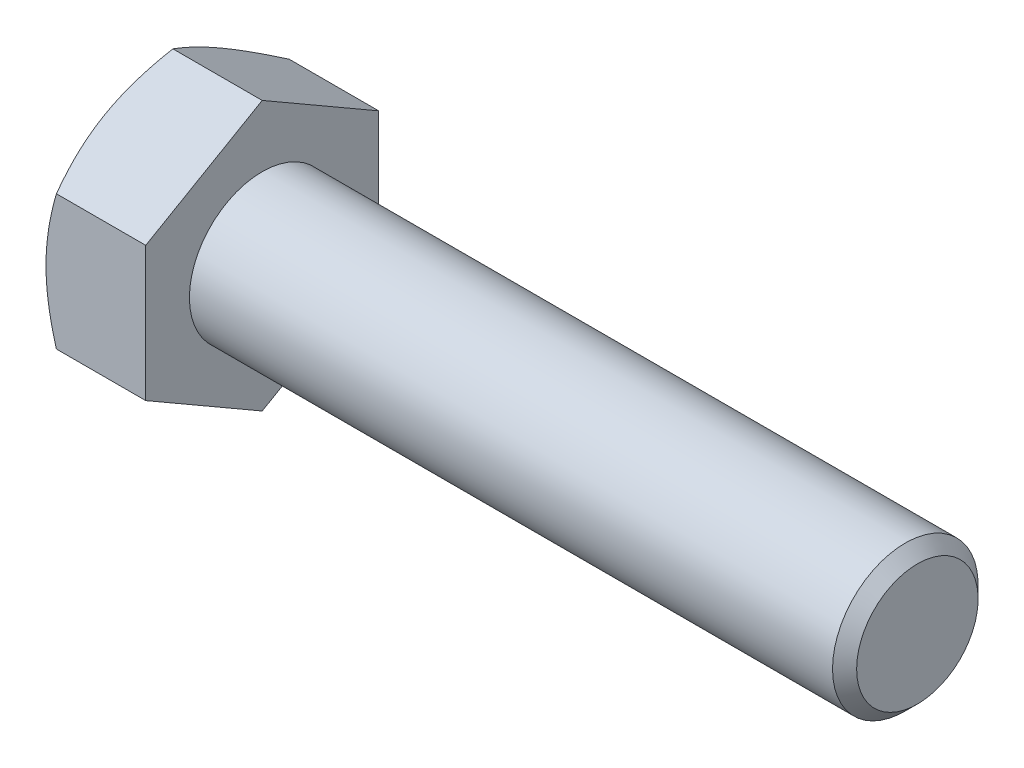
SolidWorks part; units mm, degrees
extrude "BaseHead" add sketch "Sketch1" along normal blind 6.85
sketch "Sketch1" plane through (0, 0, 0) normal (1, 0, 0) x (0, 0, -1)
  line L0 (8, 4.6188) -> (8, -4.6188)
  line L1 (-8, 4.6188) -> (-8, -4.6188)
  line L2 (8, -4.6188) -> (0, -9.2376)
  line L3 (0, -9.2376) -> (-8, -4.6188)
  line L4 (8, 4.6188) -> (0, 9.2376)
  line L5 (0, 9.2376) -> (-8, 4.6188)
  dimension "Width_flats" = 16
  dimension "D2" = 120
  dimension "D3" = 8
  dimension "D4" = 8
  dimension "D5" = 8
ref_plane "Plane1" through (0, 0, 0) normal (0, 0, 1) x (1, 0, 0)
ref_plane "Plane2" through (0, 0, 0) normal (0, 1, 0) x (1, 0, 0)
ref_plane "Plane3" through (0, 0, 0) normal (1, 0, 0) x (0, 0, -1)
sketch "BodySke" plane through (0, 0, 0) normal (0, 0, 1) x (1, 0, 0)
  line L0 (0, 4.6188) -> (0, -4.6188) construction
  line L1 (0, 0) -> (51.85, 0)
  line L2 (0, 0) -> (0, 5)
  line L3 (0, 5) -> (51.022, 5)
  line L4 (51.85, 0) -> (51.85, 4.172)
  line L5 (6.85, 9.2376) -> (6.85, 4.6188) construction
  line L6 (51.85, 4.172) -> (51.022, 5)
  line L7 (0, 0) -> (96.52, 0) construction
  line L8 (51.85, -4.172) -> (51.022, -5) construction
  line L9 (0, -5) -> (51.022, -5) construction
  line L10 (8.35, 15.24) -> (8.35, -1.27) construction
  line L11 (25.85, 15.24) -> (25.85, -1.27) construction
  line L12 (6.85, 4.6188) -> (6.85, -4.6188) construction
  dimension "Diameter" = 10
revolve "BaseBody" add sketch "BodySke"
cosmetic thread "ThreadCosmetic" [suppressed]
fillet "HeadFillet" [suppressed] radius 0.4
sketch "Sketch3" plane through (0, 0, 0) normal (0, 0, 1) x (1, 0, 0)
  line L0 (0, 8) -> (3.6013, 14.2376)
  line L1 (0, 9.2376) -> (0, 4.6188) construction
  line L2 (3.6013, 14.2376) -> (3.6013, 19.2376)
  line L3 (3.6013, 19.2376) -> (-10, 19.2376)
  line L4 (-10, 19.2376) -> (-10, 8)
  line L5 (-10, 8) -> (0, 8)
  line L6 (0, 0) -> (99.06, 0) construction
  line L7 (6.85, 9.2376) -> (0, 9.2376) construction
  dimension "D1" = 8
  dimension "D2" = 5
  dimension "D3" = 10
  dimension "D4" = 5
  dimension "Head_ch_ang" = 30
revolve "HeadChamfer" cut sketch "Sketch3" angle 360 about L6
sketch "ThdSchSke" plane through (0, 0, 0) normal (0, 0, 1) x (1, 0, 0)
  line L0 (25.85, -4.172) -> (25.2702, -5)
  line L1 (25.85, -4.172) -> (26.4298, -5)
  line L2 (26.4298, -5) -> (26.4298, -6.25)
  line L3 (-3.175, 0) -> (5.1513, 0) construction
  line L5 (26.4298, -6.25) -> (25.2702, -6.25)
  line L6 (25.2702, -6.25) -> (25.2702, -5)
  dimension "Thread_minor" = 8.344
  dimension "Diameter" = 10
  dimension "Start" = 25.85
revolve "ThreadSchematic" [suppressed] cut sketch "ThdSchSke" angle 360 about L3
pattern_linear "ThdSchPat" [suppressed]
equation "\"D3@Sketch1\" = \"Width_flats@Sketch1\" / 2"
equation "\"D4@Sketch1\" = \"D3@Sketch1\""
equation "\"D5@Sketch1\" = \"D4@Sketch1\""
equation "\"Thread_minor@ThreadCosmetic\" = \"Minor_dia@BodySke\""
equation "\"D1@Sketch3\" = \"Width_flats@Sketch1\" / 2"
equation "' \"D1@Sketch4\" = \"Width_flats@Sketch1\""
equation "\"Thread_length@ThreadCosmetic\" = ((sgn( (\"Length@BodySke\" - \"Advance@BodySke\" ) - \"Thread_nom@BodySke\" )-1)*( (\"Length@BodySke\" - \"Advance@BodySke\" ) - \"Thread_nom@BodySke\" ))/-2+ \"Thread_nom@BodySke\""
equation "\"Thread_minor@ThdSchSke\" = \"Minor_dia@BodySke\""
equation "\"Diameter@ThdSchSke\" = \"Diameter@BodySke\""
equation "\"Overcut@ThdSchSke\" = \"Diameter@BodySke\" * 1.25"
equation "\"Start@ThdSchSke\" = \"Head_ht@BaseHead\" + \"Length@BodySke\" - \"Thread_length@ThreadCosmetic\"  '---Non-countersunk---"
equation "\"Num_threads@ThdSchPat\" = int( \"Thread_length@ThreadCosmetic\" / \"Advance@BodySke\" + 0.999 )  + 1"
equation "\"Advance@ThdSchPat\" = \"Thread_length@ThreadCosmetic\" /  (\"Num_threads@ThdSchPat\" - 1) 'relax it"
equation "\"Num_threads@ThdSchPat\" = \"Num_threads@ThdSchPat\" - sgn( \"Num_threads@ThdSchPat\" - 1) '---chamfered tips only---"
